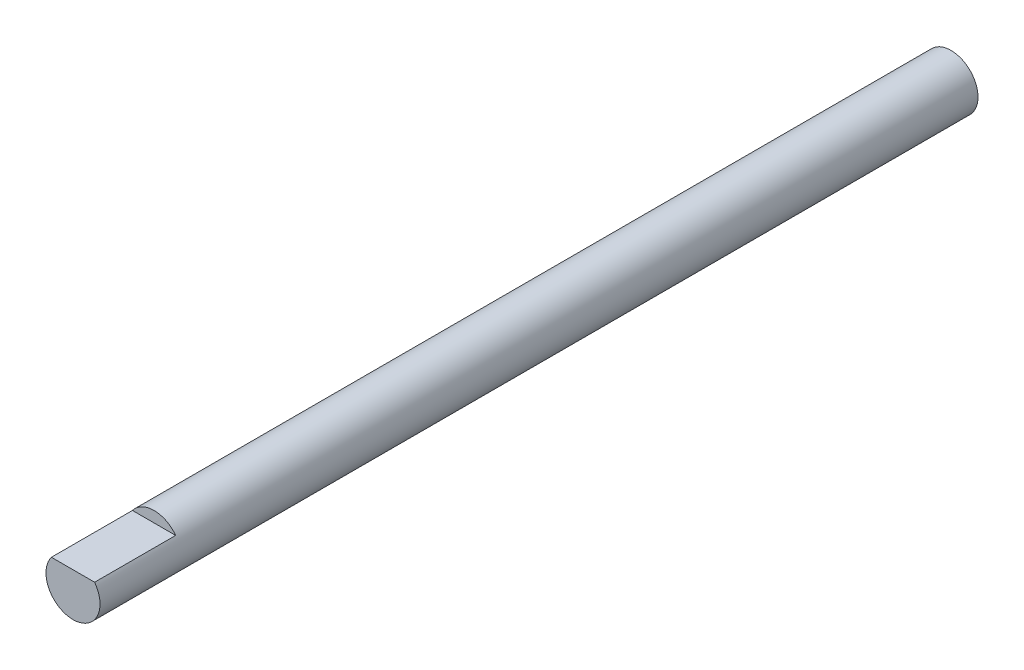
SolidWorks part; units mm, degrees
ref_plane "Alzado" through (0, 0, 0) normal (0, 0, 1) x (1, 0, 0)
ref_plane "Planta" through (0, 0, 0) normal (0, 1, 0) x (1, 0, 0)
ref_plane "Vista lateral" through (0, 0, 0) normal (1, 0, 0) x (0, 0, -1)
sketch "Croquis1" plane through (0, 0, 0) normal (0, 0, 1) x (1, 0, 0)
  circle A0 centre (0, 0) radius 4
extrude "Saliente-Extruir1" add sketch "Croquis1" along normal blind 130
sketch "Croquis2" plane through (0, 0, 130) normal (0, 0, 1) x (1, 0, 0)
  line L0 (0, -4) -> (0, 2.4) construction
  line L1 (-3.2, 2.4) -> (3.2, 2.4)
  circle A0 centre (0, 0) radius 4 construction
  arc A1 (-3.2, 2.4) -> (3.2, 2.4) centre (0, 0) cw
extrude "Cortar-Extruir1" cut sketch "Croquis2" against normal blind 12 contours A1 L1
